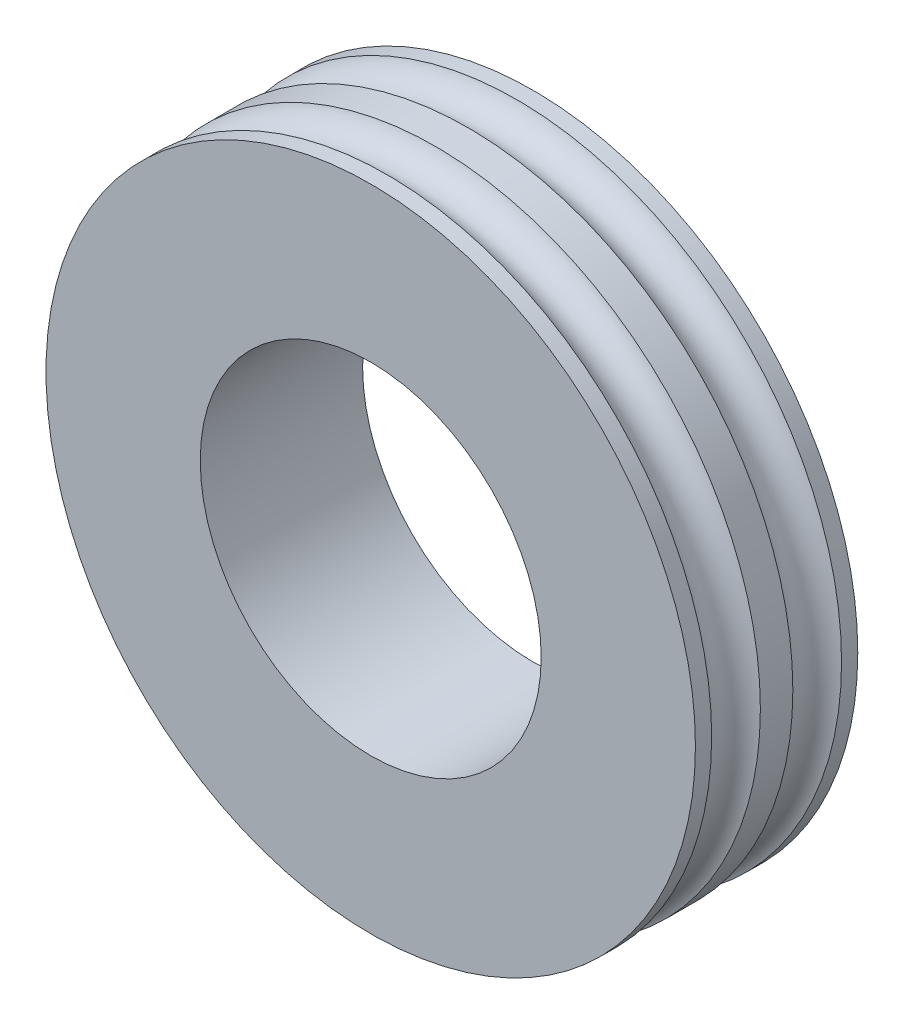
SolidWorks part; units mm, degrees
ref_plane "Front Plane" through (0, 0, 0) normal (0, 0, 1) x (1, 0, 0)
ref_plane "Top Plane" through (0, 0, 0) normal (0, 1, 0) x (1, 0, 0)
ref_plane "Right Plane" through (0, 0, 0) normal (1, 0, 0) x (0, 0, -1)
sketch "Sketch2" plane through (0, 0, 0) normal (1, 0, 0) x (0, 0, -1)
  line L0 (0, 2.1) -> (0, 4)
  line L1 (0, 4) -> (-0.2, 4)
  line L2 (-1, 4) -> (-1, 2.1)
  line L4 (-1, 2.1) -> (0, 2.1)
  line L5 (-3.0147, 0) -> (3.0268, 0) construction
  line L6 (-0.8, 4) -> (-1, 4)
  arc A0 (-0.8, 4) -> (-0.2, 4) centre (-0.5, 4.1) ccw
  dimension "D6" = 0.1
  dimension "D1" = 2.1
  dimension "D2" = 1
  dimension "D3" = 4
  dimension "D4" = 0.2
  dimension "D5" = 0.2
revolve "Revolve1" add sketch "Sketch2" angle 360 about L5
ref_plane "Plane1" through (0, 0, 0) normal (0, 0, -1) x (-1, 0, 0)
mirror "Mirror2" about plane through (0, 0, 0) normal (0, 0, -1) of "Revolve1"
